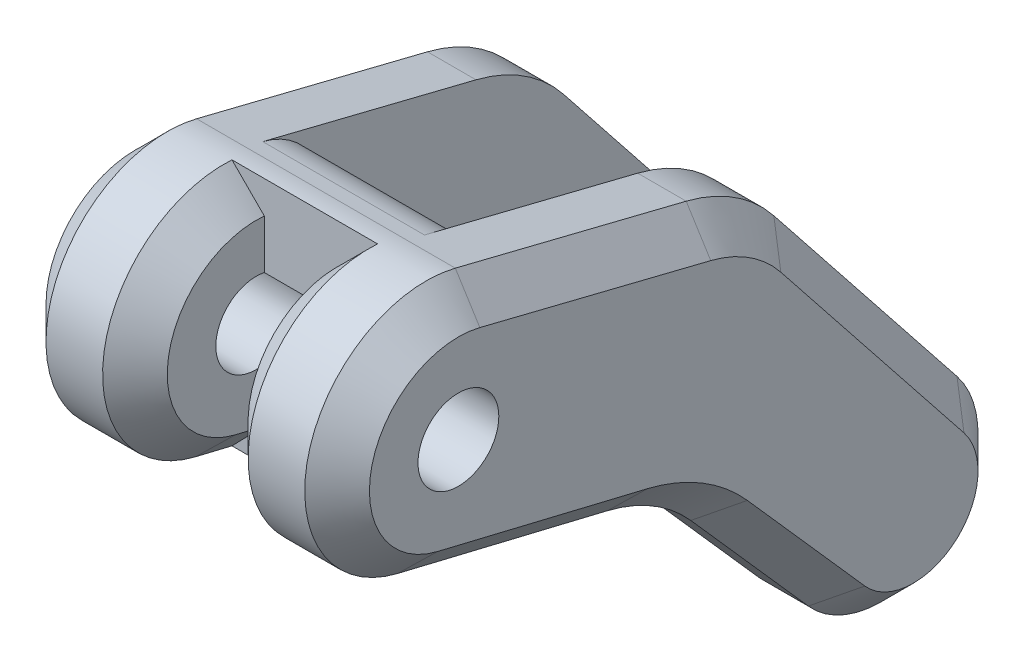
SolidWorks part; units mm, degrees
material "1060 Alloy"
ref_plane "Front Plane" through (0, 0, 0) normal (0, 0, 1) x (1, 0, 0)
ref_plane "Top Plane" through (0, 0, 0) normal (0, 1, 0) x (1, 0, 0)
ref_plane "Right Plane" through (0, 0, 0) normal (1, 0, 0) x (0, 0, -1)
sketch "Sketch1" plane through (0, 0, 0) normal (1, 0, 0) x (0, 0, -1)
  line L0 (-26.3209, 25.0365) -> (-12.0438, 21.4842)
  line L1 (-6.6261, 17.9974) -> (4.6994, 3.7304)
  line L2 (-29.8878, 10.4669) -> (-16.9109, 7.3417)
  line L3 (-11.7604, 4.2433) -> (-4.4951, -3.9742)
  circle A0 centre (0, 0) radius 2.5
  arc A1 (-4.4951, -3.9742) -> (4.6994, 3.7304) centre (0, 0) ccw
  arc A2 (-26.3209, 25.0365) -> (-29.8878, 10.4669) centre (-28.1318, 17.7584) ccw
  circle A3 centre (-28.1318, 17.7584) radius 2.5
  arc A4 (-16.9109, 7.3417) -> (-11.7604, 4.2433) centre (-19.2522, -2.3804) cw
  arc A5 (-12.0438, 21.4842) -> (-6.6261, 17.9974) centre (-14.4583, 11.7801) cw
  dimension "D1" = 5
  dimension "D2" = 12
  dimension "D3" = 5
  dimension "D4" = 10
  dimension "D5" = 15
extrude "Boss-Extrude1" add sketch "Sketch1" along normal blind 20 contours L1 A1 L3 A4 L2 A2 L0 A5
sketch "Sketch2" plane through (0, 0, 0) normal (0, 1, 0) x (1, 0, 0)
  line L0 (20, -12.0438) -> (20, -6.6261) construction
  line L1 (5, 9.8192) -> (15, 9.8192)
  line L2 (5, 9.8192) -> (5, -21.4339)
  line L3 (5, -21.4339) -> (15, -21.4339)
  line L4 (15, 9.8192) -> (15, -21.4339)
  dimension "D1" = 10
  dimension "D2" = 5
extrude "Cut-Extrude1" cut sketch "Sketch2" against normal through all both and the other way through all
fillet "Fillet1" radius 5 2 edges at (10, 23.8205, 21.4339) (10, 8.4309, 21.4339)
chamfer "Chamfer1" distance 2 angle 45 16 edges at (0, 10.8639, 0.9634) (0, 20.1891, 9.0464) (0, -4.5988, -3.8537) (0, 23.2603, 19.1824) (0, 0.1346, 8.1277) (0, 19.5418, 35.4167) (0, 6.1886, 14.0974) (0, 8.9043, 23.3993) (20, 10.8639, 0.9634) (20, 20.1891, 9.0464) (20, -4.5988, -3.8537) (20, 23.2603, 19.1824) (20, 0.1346, 8.1277) (20, 19.5418, 35.4167) (20, 6.1886, 14.0974) (20, 8.9043, 23.3993)
sketch "Sketch4" plane through (20, 0, 0) normal (1, 0, 0) x (0, 0, -1)
  circle A0 centre (0, 0) radius 2.5
  circle A1 centre (0, 0) radius 2.5 construction
extrude "Boss-Extrude2" add sketch "Sketch4" against normal up to surface (20 mm away) up to face at (0, 10.7073, 13.232)
sketch "Sketch5" plane through (0, 0, 0) normal (0, 1, 0) x (1, 0, 0)
  line L0 (20, -33.6318) -> (20, -26.8038) construction
  line L1 (7.5, -27.6318) -> (12.5, -27.6318)
  line L2 (7.5, -27.6318) -> (7.5, -35.6318)
  line L3 (7.5, -35.6318) -> (12.5, -35.6318)
  line L4 (12.5, -27.6318) -> (12.5, -35.6318)
  line L5 (2, -35.6318) -> (18, -35.6318) construction
  dimension "D1" = 5
  dimension "D2" = 7.5
  dimension "D3" = 8
extrude "Cut-Extrude2" cut sketch "Sketch5" against normal through all both and the other way through all
chamfer "Chamfer2" distance 2 angle 45 4 edges at (12.5, 10.1952, 28.7598) (12.5, 18.8905, 35.5459) (7.5, 10.1952, 28.7598) (7.5, 18.8905, 35.5459)
scale "Scale1" scale about centroid uniform scaling yes scale factor 2
